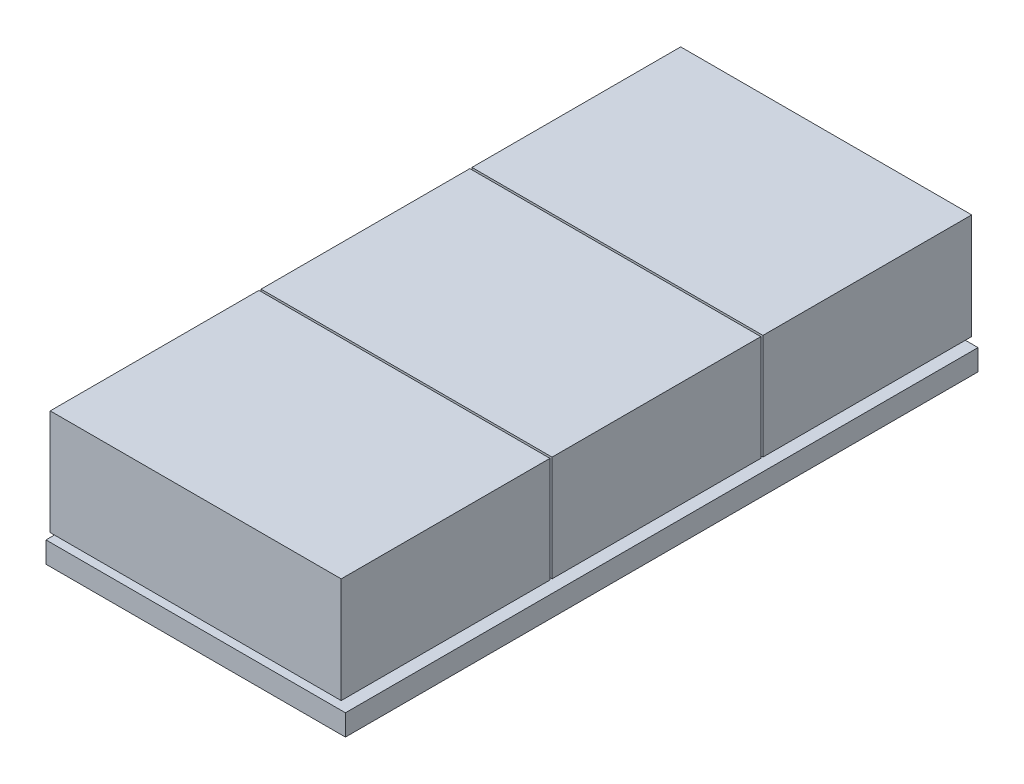
SolidWorks part; units mm, degrees
ref_plane "Front Plane" through (0, 0, 0) normal (0, 0, 1) x (1, 0, 0)
ref_plane "Top Plane" through (0, 0, 0) normal (0, 1, 0) x (1, 0, 0)
ref_plane "Right Plane" through (0, 0, 0) normal (1, 0, 0) x (0, 0, -1)
sketch "Sketch1" plane through (0, 0, 0) normal (0, 1, 0) x (1, 0, 0)
  line L1 (-35.5, -75) -> (35.5, -75)
  line L2 (-35.5, -75) -> (-35.5, 75)
  line L3 (-35.5, 75) -> (35.5, 75)
  line L4 (35.5, -75) -> (35.5, 75)
  line L5 (-35.5, -75) -> (35.5, 75) construction
  line L6 (-35.5, 75) -> (35.5, -75) construction
  point P0 (0, 0)
  dimension "D1" = 71
  dimension "D2" = 150
extrude "Boss-Extrude1" add sketch "Sketch1" along normal blind 5
sketch "Sketch2" plane through (0, 5, 0) normal (0, 1, 0) x (1, 0, 0)
  line L0 (0, 0) -> (0, -75) construction
  line L1 (-35.5, -75) -> (35.5, -75) construction
  line L3 (-32.5, -27.5) -> (32.5, -27.5)
  line L4 (-32.5, -27.5) -> (-32.5, -72.5)
  line L5 (-32.5, -72.5) -> (32.5, -72.5)
  line L6 (32.5, -27.5) -> (32.5, -72.5)
  line L7 (-32.5, -27.5) -> (32.5, -72.5) construction
  line L8 (-32.5, -72.5) -> (32.5, -27.5) construction
  point P5 (0, -50)
  dimension "D1" = 65
  dimension "D2" = 45
  dimension "D3" = 2.5
extrude "Boss-Extrude3" add sketch "Sketch2" along normal blind 2
pattern_linear "LPattern1" count 3 spacing 50 along (0, 0, -1) of "Boss-Extrude3"
sketch "Sketch3" plane through (0, 7, 0) normal (0, 1, 0) x (1, 0, 0)
  line L0 (0, 0) -> (0, -72.5) construction
  line L1 (-32.5, -72.5) -> (32.5, -72.5) construction
  line L2 (-35.5, 75) -> (-35.5, -75) construction
  line L3 (-34.5, -25.5) -> (34.5, -25.5)
  line L4 (-34.5, -25.5) -> (-34.5, -75)
  line L5 (-34.5, -75) -> (34.5, -75)
  line L6 (34.5, -25.5) -> (34.5, -75)
  line L7 (-34.5, -25.5) -> (34.5, -75) construction
  line L8 (-34.5, -75) -> (34.5, -25.5) construction
  line L9 (-32.5, -22.5) -> (32.5, -22.5) construction
  dimension "D1" = 1
  dimension "D2" = 49.5
  dimension "D3" = 3
extrude "Boss-Extrude8" add sketch "Sketch3" along normal blind 25
pattern_linear "LPattern5" count 3 spacing 50 along (0, 0, -1) of "Boss-Extrude8"
